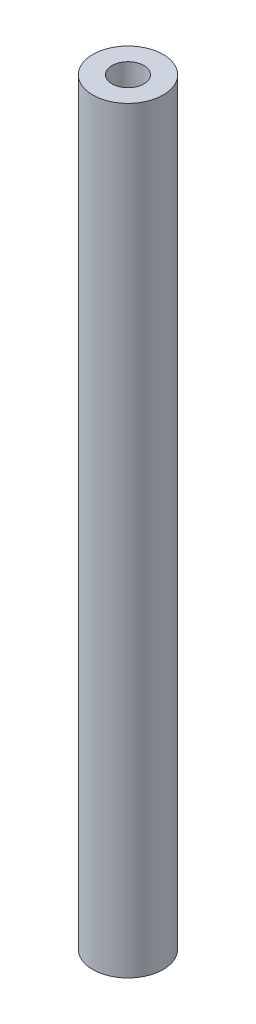
SolidWorks part; units mm, degrees
ref_plane "Front Plane" through (0, 0, 0) normal (0, 0, 1) x (1, 0, 0)
ref_plane "Top Plane" through (0, 0, 0) normal (0, 1, 0) x (1, 0, 0)
ref_plane "Right Plane" through (0, 0, 0) normal (1, 0, 0) x (0, 0, -1)
sketch "Sketch1" plane through (0, 0, 0) normal (0, 1, 0) x (1, 0, 0)
  circle A0 centre (0, 0) radius 4.7625
  circle A1 centre (0, 0) radius 2.159
  dimension "D1" = 9.525
  dimension "D2" = 4.318
extrude "Boss-Extrude1" add sketch "Sketch1" along normal blind 102.616
